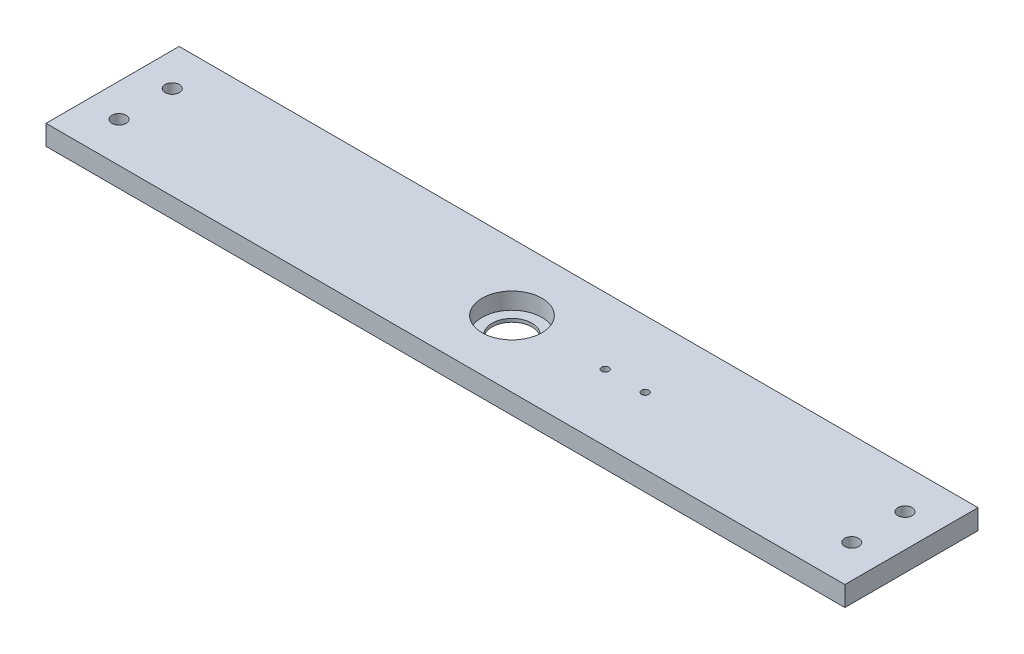
SolidWorks part; units mm, degrees
material "6061-T6 (SS)"
ref_plane "Front Plane" through (0, 0, 0) normal (0, 0, 1) x (1, 0, 0)
ref_plane "Top Plane" through (0, 0, 0) normal (0, 1, 0) x (1, 0, 0)
ref_plane "Right Plane" through (0, 0, 0) normal (1, 0, 0) x (0, 0, -1)
sketch "Sketch1" plane through (0, 0, 0) normal (0, 1, 0) x (1, 0, 0)
  line L1 (-190.5, -31.75) -> (190.5, -31.75)
  line L2 (-190.5, -31.75) -> (-190.5, 31.75)
  line L3 (-190.5, 31.75) -> (190.5, 31.75)
  line L4 (190.5, -31.75) -> (190.5, 31.75)
  line L5 (-190.5, -31.75) -> (190.5, 31.75) construction
  line L6 (-190.5, 31.75) -> (190.5, -31.75) construction
  point P0 (0, 0)
  dimension "D1" = 381
  dimension "D2" = 63.5
extrude "Boss-Extrude1" add sketch "Sketch1" along normal blind 9.525
sketch "Sketch2" plane through (0, 9.525, 0) normal (0, 1, 0) x (1, 0, 0)
  circle A0 centre (0, 0) radius 14.2875
  dimension "D1" = 28.575
extrude "Cut-Extrude1" cut sketch "Sketch2" against normal blind 7.9375
hole_wizard "1/4 Clearance Hole1" positions "Sketch4" profile "Sketch5" hole size "1/4" standard "ANSI Inch" end condition through all
sketch "Sketch4" plane through (0, 9.525, 0) normal (0, 1, 0) x (1, 0, 0)
  line L6 (-174.7388, -12.7) -> (-190.5, -31.75)
  line L9 (-174.7388, 12.7) -> (-190.5, 31.75)
  line L14 (190.5, 31.75) -> (174.7388, 12.7)
  line L17 (174.7388, -12.7) -> (190.5, -31.75)
  point P0 (-174.7388, 12.7)
  point P2 (174.7388, 12.7)
  point P24 (-174.7388, -12.7)
  point P26 (174.7388, -12.7)
  dimension "D1" = 349.4776
  dimension "D2" = 25.4
sketch "Sketch5" plane through (-174.7388, 9.525, -12.7) normal (1, 0, 0) x (0, 0, 1)
  line L0 (0, 0) -> (0, 9.525)
  line L1 (0, 9.525) -> (3.3782, 9.525)
  line L2 (3.3782, 9.525) -> (3.3782, 0)
  line L5 (3.3782, 0) -> (0, 0)
  line L11 (0, -6.35) -> (0, 107.95) construction
  dimension "Thru Hole Dia." = 6.7564
  dimension "Thru Hole Depth" = 9.525
hole_wizard "#8-32 Tapped Hole1" positions "Sketch6" profile "Sketch7" tap size "#8-32" standard "ANSI Inch" end condition through all
sketch "Sketch6" plane through (0, 9.525, 0) normal (0, 1, 0) x (1, 0, 0)
  point P0 (63.5, 0)
  point P2 (44.45, 0)
  dimension "D1" = 44.45
  dimension "D2" = 19.05
sketch "Sketch7" plane through (63.5, 9.525, 0) normal (1, 0, 0) x (0, 0, 1)
  line L0 (0, 0) -> (0, 9.525)
  line L1 (0, 9.525) -> (1.7272, 9.525)
  line L2 (1.7272, 9.525) -> (1.7272, 0)
  line L5 (1.7272, 0) -> (0, 0)
  line L11 (0, -6.35) -> (0, 107.95) construction
  dimension "Thru Tap Drill Dia." = 3.4544
  dimension "Thru Tap Drill Depth" = 9.525
cosmetic thread "Hole Thread1" parameters "D2"=4.1656
cosmetic thread "Hole Thread2" parameters "D2"=4.1656
sketch "Sketch8" plane through (0, 1.5875, 0) normal (0, 1, 0) x (1, 0, 0)
  circle A0 centre (0, 0) radius 9.525
  dimension "D1" = 19.05
extrude "Cut-Extrude2" cut sketch "Sketch8" against normal through all
